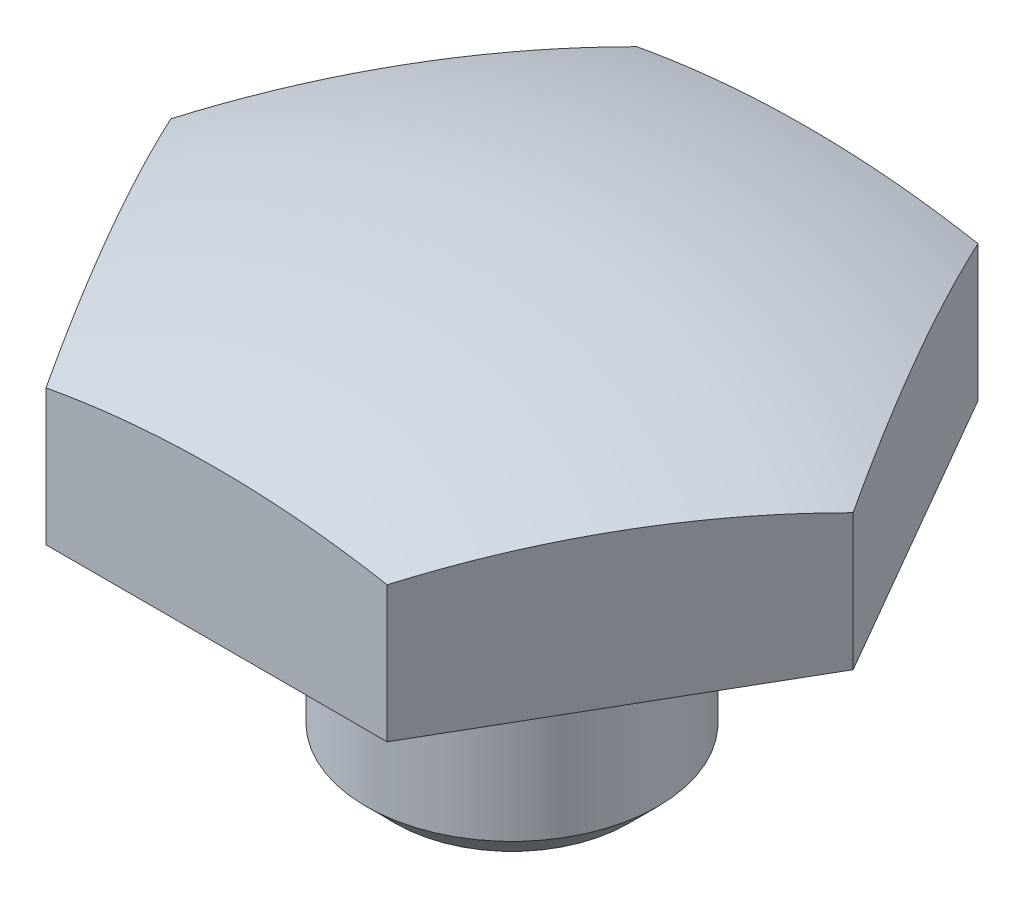
SolidWorks part; units mm, degrees
ref_plane "Front Plane" through (0, 0, 0) normal (0, 0, 1) x (1, 0, 0)
ref_plane "Top Plane" through (0, 0, 0) normal (0, 1, 0) x (1, 0, 0)
ref_plane "Right Plane" through (0, 0, 0) normal (1, 0, 0) x (0, 0, -1)
sketch "Sketch3" plane through (0, 0, 0) normal (0, 0, 1) x (1, 0, 0)
  line L1 (4.699, 4.9911) -> (4.699, 0.9525)
  line L2 (10.9985, 7.9248) -> (4.1275, 7.9248)
  line L3 (3.7465, 7.5438) -> (3.7465, 5.9436)
  line L4 (3.7465, 5.9436) -> (4.699, 4.9911)
  line L5 (0, 14.2748) -> (0, 0)
  line L6 (4.699, 0.9525) -> (3.7465, 0)
  line L7 (10.9985, 12.3089) -> (10.9985, 7.9248)
  line L8 (0, 0) -> (3.7465, 0)
  line L10 (0, -1000) -> (0, 49000) construction
  arc A0 (4.1275, 7.9248) -> (3.7465, 7.5438) centre (4.1275, 7.5438) ccw
  arc A1 (10.9985, 12.3089) -> (0, 14.2748) centre (0, -17.4752) ccw
  dimension "D10" = 0.381
  dimension "D3" = 63.5
  dimension "D1" = 1.9812
  dimension "D2" = 7.9248
  dimension "D4" = 21.997
  dimension "D5" = 45
  dimension "D6" = 45
  dimension "D7" = 9.398
  dimension "D8" = 7.493
  dimension "D9" = 14.2748
revolve "Revolve1" add sketch "Sketch3" angle 360 about L10
cosmetic thread "3/8-24 UNF" parameters "D2"=8.763
sketch "Sketch1" plane through (0, 0, 0) normal (0, 1, 0) x (1, 0, 0)
  line L1 (10.9985, 0) -> (5.4993, 9.525)
  line L2 (5.4993, 9.525) -> (-5.4993, 9.525)
  line L3 (-5.4993, 9.525) -> (-10.9985, 0)
  line L4 (-10.9985, 0) -> (-5.4993, -9.525)
  line L5 (-5.4993, -9.525) -> (5.4993, -9.525)
  line L6 (5.4993, -9.525) -> (10.9985, 0)
  circle A0 centre (0, 0) radius 9.525 construction
  circle A1 centre (0, 0) radius 10.9985
  dimension "D1" = 19.05
extrude "Cut-Extrude2" cut sketch "Sketch1" along normal blind 14.2748 contours L5 A1 | L4 A1 | L6 A1 | L1 A1 | L2 A1 | L3 A1
